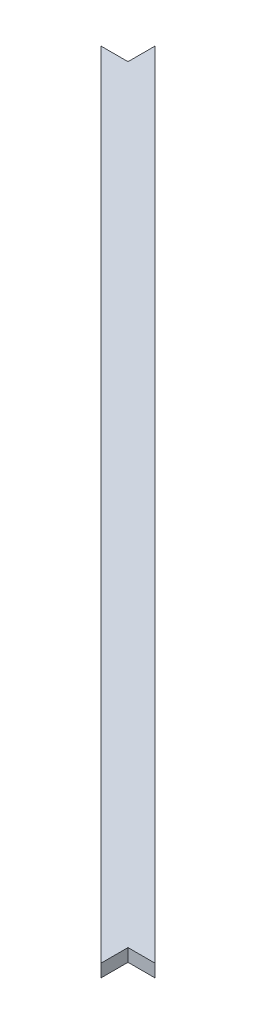
SolidWorks part; units mm, degrees
ref_plane "Front Plane" through (0, 0, 0) normal (0, 0, 1) x (1, 0, 0)
ref_plane "Top Plane" through (0, 0, 0) normal (0, 1, 0) x (1, 0, 0)
ref_plane "Right Plane" through (0, 0, 0) normal (1, 0, 0) x (0, 0, -1)
sketch "Sketch1" plane through (0, 0, 0) normal (0, 1, 0) x (1, 0, 0)
  line L0 (367.4796, -394.4204) -> (394.4204, -367.4796) construction
  line L5 (-419.05, -419.05) -> (419.05, -419.05) construction
  line L6 (-419.05, -419.05) -> (-419.05, 419.05) construction
  line L15 (-419.05, 419.05) -> (419.05, 419.05) construction
  line L16 (419.05, -419.05) -> (419.05, 419.05) construction
  line L23 (-419.05, -419.05) -> (419.05, 419.05) construction
  line L24 (-419.05, 419.05) -> (419.05, -419.05) construction
  line L25 (-419.05, 419.05) -> (-380.95, 419.05) construction
  line L26 (-419.05, 419.05) -> (-419.05, 380.95) construction
  line L27 (-419.05, 380.95) -> (-380.95, 380.95) construction
  line L28 (-380.95, 419.05) -> (-380.95, 380.95) construction
  line L29 (419.05, -419.05) -> (380.95, -419.05) construction
  line L30 (419.05, -419.05) -> (419.05, -380.95) construction
  line L31 (419.05, -380.95) -> (380.95, -380.95) construction
  line L32 (380.95, -419.05) -> (380.95, -380.95) construction
  line L33 (394.4204, -367.4796) -> (311.3933, -284.4525) construction
  line L34 (367.4796, -394.4204) -> (326.6872, -353.6279) construction
  line L35 (-380.95, 407.8908) -> (-380.95, 380.95)
  line L36 (-380.95, 380.95) -> (-407.8908, 380.95)
  line L37 (-407.8908, 380.95) -> (380.95, -407.8908)
  line L38 (380.95, -407.8908) -> (380.95, -380.95)
  line L39 (380.95, -380.95) -> (407.8908, -380.95)
  line L40 (407.8908, -380.95) -> (-380.95, 407.8908)
  point P0 (0, 0)
  point P3 (0, 0)
  point P16 (380.95, -380.95)
  point P19 (380.95, -407.8908)
  point P21 (407.8908, -380.95)
  point P22 (-407.8908, 380.95)
  point P23 (-380.95, 407.8908)
  dimension "D1" = 838.1
  dimension "D2" = 838.1
  dimension "D3" = 38.1
  dimension "D4" = 38.1
  dimension "D5" = 38.1
  dimension "D6" = 38.1
extrude "Boss-Extrude1" add sketch "Sketch1" along normal blind 12.7
